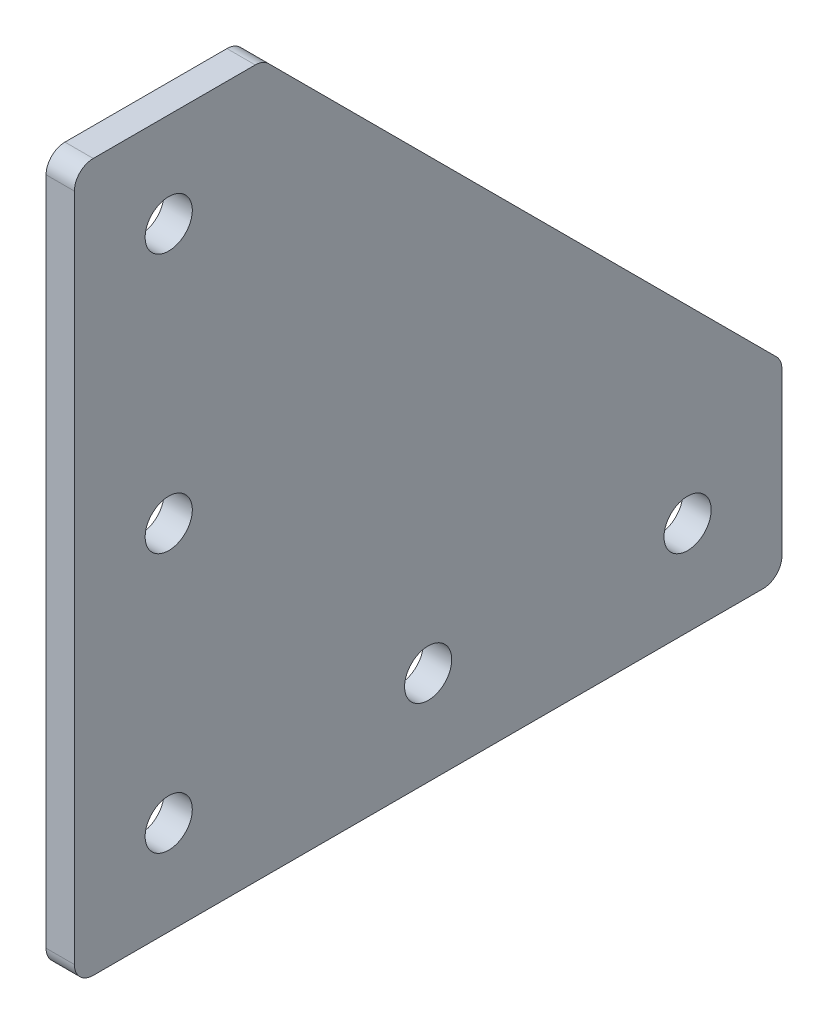
SolidWorks part; units mm, degrees
ref_plane "Front Plane" through (0, 0, 0) normal (0, 0, 1) x (1, 0, 0)
ref_plane "Top Plane" through (0, 0, 0) normal (0, 1, 0) x (1, 0, 0)
ref_plane "Right Plane" through (0, 0, 0) normal (1, 0, 0) x (0, 0, -1)
sketch "Sketch1" plane through (0, 0, 0) normal (1, 0, 0) x (0, 0, -1)
  line L0 (75, 0) -> (0, 0)
  line L1 (0, 0) -> (0, 75)
  line L2 (0, 75) -> (20, 75)
  line L3 (20, 75) -> (75, 20)
  line L4 (75, 20) -> (75, 0)
  line L5 (0, 0) -> (47.5, 47.5) construction
  line L6 (10, 10) -> (37.5, 10) construction
  line L7 (37.5, 10) -> (65, 10) construction
  circle A0 centre (65, 10) radius 2.5
  circle A1 centre (37.5, 10) radius 2.5
  circle A2 centre (10, 10) radius 2.5
  circle A3 centre (10, 65) radius 2.5
  circle A4 centre (10, 37.5) radius 2.5
  point P15 (37.5, 0)
  dimension "D5" = 5
  dimension "D1" = 75
  dimension "D2" = 75
  dimension "D3" = 20
  dimension "D4" = 20
  dimension "D6" = 10
extrude "Boss-Extrude1" add sketch "Sketch1" along normal blind 3
fillet "Fillet1" radius 2 5 edges at (1.5, 0, 0) (1.5, 0, -75) (1.5, 20, -75) (1.5, 75, -20) (1.5, 75, 0)
